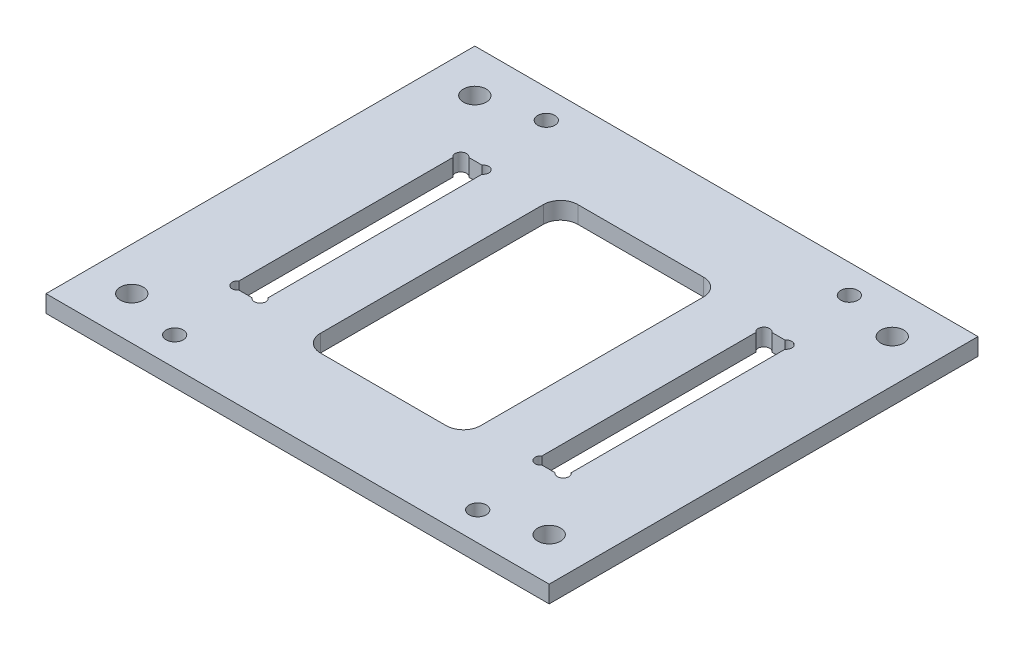
SolidWorks part; units mm, degrees
material "3.1325 (EN-AW 2017A)"
ref_plane "正面" through (0, 0, 0) normal (0, 0, 1) x (1, 0, 0)
ref_plane "平面" through (0, 0, 0) normal (0, 1, 0) x (1, 0, 0)
ref_plane "右側面" through (0, 0, 0) normal (1, 0, 0) x (0, 0, -1)
sketch "ｽｹｯﾁ1" plane through (0, 0, 0) normal (0, 1, 0) x (1, 0, 0)
  line L1 (-44, -37.5) -> (44, -37.5)
  line L2 (-44, -37.5) -> (-44, 37.5)
  line L3 (-44, 37.5) -> (44, 37.5)
  line L4 (44, -37.5) -> (44, 37.5)
  line L5 (-44, -37.5) -> (44, 37.5) construction
  line L6 (-44, 37.5) -> (44, -37.5) construction
  point P0 (0, 0)
  dimension "D1" = 75
  dimension "D2" = 88
extrude "ﾎﾞｽ - 押し出し1" add sketch "ｽｹｯﾁ1" along normal blind 3
sketch "ｽｹｯﾁ2" plane through (0, 3, 0) normal (0, 1, 0) x (1, 0, 0)
  line L0 (-23.95, 0) -> (23.95, 0) construction
  line L1 (-29.05, 20.1) -> (-23.95, 20.1)
  line L2 (-29.05, 20.1) -> (-29.05, -20.1)
  line L3 (-29.05, -20.1) -> (-23.95, -20.1)
  line L4 (-23.95, 20.1) -> (-23.95, -20.1)
  line L5 (23.95, 20.1) -> (29.05, 20.1)
  line L6 (23.95, 20.1) -> (23.95, -20.1)
  line L7 (23.95, -20.1) -> (29.05, -20.1)
  line L8 (29.05, 20.1) -> (29.05, -20.1)
  line L9 (-44, 37.5) -> (-44, -37.5) construction
  line L10 (-44, -37.5) -> (44, -37.5) construction
  line L11 (44, -37.5) -> (44, 37.5) construction
  line L12 (44, 37.5) -> (-44, 37.5) construction
  line L14 (-26.5, 32.5) -> (-26.5, -32.5) construction
  line L15 (26.5, 32.5) -> (26.5, -32.5) construction
  line L16 (14, -22.5) -> (-14, -22.5)
  line L17 (14, -22.5) -> (14, 22.5)
  line L18 (14, 22.5) -> (-14, 22.5)
  line L19 (-14, -22.5) -> (-14, 22.5)
  line L20 (14, -22.5) -> (-14, 22.5) construction
  line L21 (14, 22.5) -> (-14, -22.5) construction
  circle A0 centre (-28.45, -19.5) radius 1
  circle A1 centre (-24.55, -19.5) radius 1
  circle A2 centre (-24.55, 19.5) radius 1
  circle A3 centre (-28.45, 19.5) radius 1
  circle A4 centre (28.45, 19.5) radius 1
  circle A5 centre (24.55, 19.5) radius 1
  circle A6 centre (24.55, -19.5) radius 1
  circle A7 centre (28.45, -19.5) radius 1
  circle A8 centre (-26.5, -32.5) radius 1.5
  circle A9 centre (26.5, -32.5) radius 1.5
  circle A10 centre (26.5, 32.5) radius 1.5
  circle A11 centre (-26.5, 32.5) radius 1.5
  circle A12 centre (-36.5, -30) radius 2
  circle A13 centre (36.5, -30) radius 2
  circle A14 centre (36.5, 30) radius 2
  circle A15 centre (-36.5, 30) radius 2
  point P33 (-26.5, -20.1)
  point P34 (26.5, -20.1)
  point P53 (0, 0)
  dimension "D11" = 5
  dimension "D12" = 2
  dimension "D13" = 3
  dimension "D16" = 5
  dimension "D17" = 0.6
  dimension "D18" = 0.6
  dimension "D6" = 0.6
  dimension "D19" = 0.6
  dimension "D20" = 0.6
  dimension "D21" = 0.6
  dimension "D22" = 7.5
  dimension "D23" = 4
  dimension "D24" = 7.5
  dimension "D27" = 7.5
  dimension "D28" = 7.5
  dimension "D29" = 7.5
  dimension "D31" = 28
  dimension "D2" = 40.2
  dimension "D3" = 5.1
  dimension "D4" = 5.1
  dimension "D5" = 40.2
  dimension "D7" = 0.6
  dimension "D30" = 26.5
  dimension "D32" = 45
  dimension "D8" = 2
  dimension "D9" = 2
  dimension "D10" = 2
  dimension "D14" = 2
  dimension "D15" = 2
  dimension "D25" = 2
  dimension "D26" = 2
extrude "ｶｯﾄ - 押し出し1" cut sketch "ｽｹｯﾁ2" against normal blind 3 contours A11 | A10 | A0 | A1 | L3 L4 L1 L2 | A3 | A2 | L8 L7 L6 L5 | A5 | A4 | A6 | A7 | A8 | A9 | A12 | A15 | A14 | A13 | L17 L16 L19 L18
fillet "ﾌｨﾚｯﾄ1" radius 3 4 edges at (-14, 1.5, 22.5) (14, 1.5, 22.5) (14, 1.5, -22.5) (-14, 1.5, -22.5)
